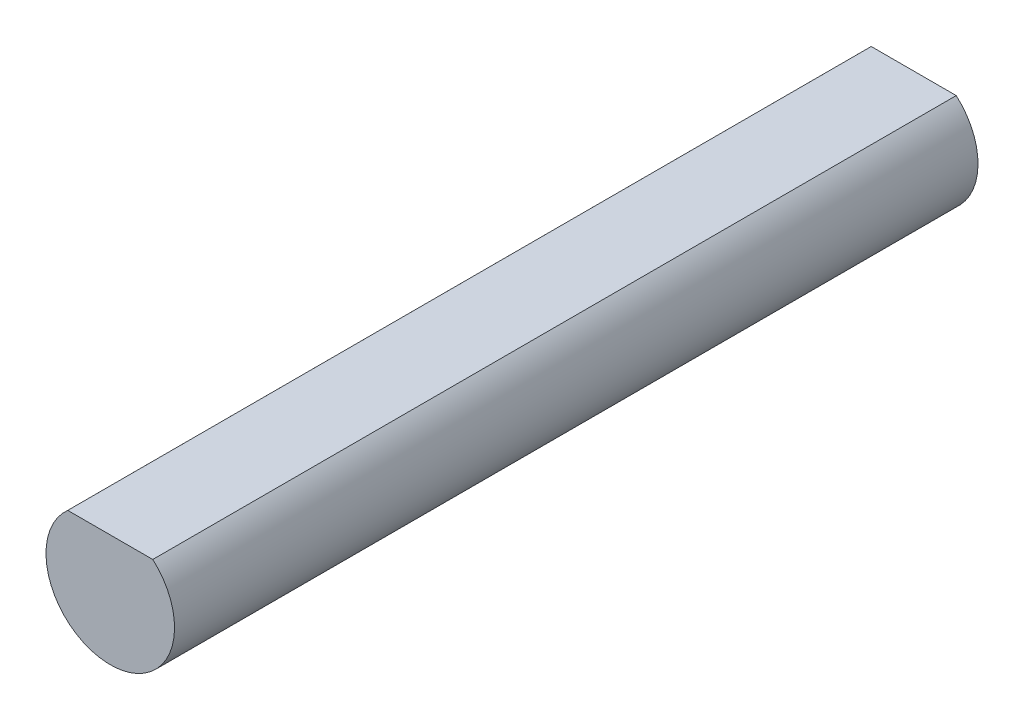
SolidWorks part; units mm, degrees
ref_plane "Front Plane" through (0, 0, 0) normal (0, 0, 1) x (1, 0, 0)
ref_plane "Top Plane" through (0, 0, 0) normal (0, 1, 0) x (1, 0, 0)
ref_plane "Right Plane" through (0, 0, 0) normal (1, 0, 0) x (0, 0, -1)
sketch "Sketch1" plane through (0, 0, 0) normal (0, 0, 1) x (1, 0, 0)
  line L0 (0, 0) -> (0, 1.5) construction
  line L1 (-1.3229, 1.5) -> (1.3229, 1.5)
  arc A0 (-1.3229, 1.5) -> (1.3229, 1.5) centre (0, 0) ccw
  dimension "D2" = 2
  dimension "D1" = 1.5
extrude "Boss-Extrude1" add sketch "Sketch1" along normal blind 25
